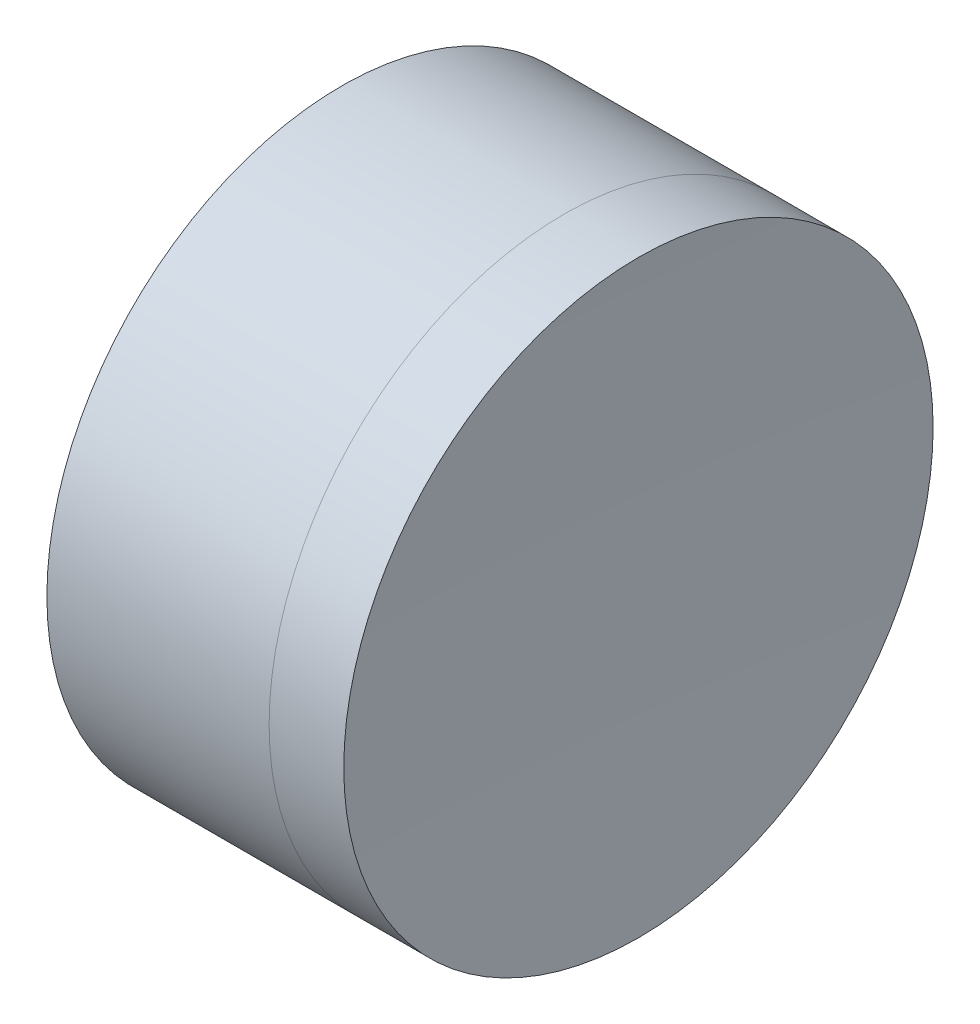
SolidWorks part; units mm, degrees
ref_plane "前视基准面" through (0, 0, 0) normal (0, 0, 1) x (1, 0, 0)
ref_plane "上视基准面" through (0, 0, 0) normal (0, 1, 0) x (1, 0, 0)
ref_plane "右视基准面" through (0, 0, 0) normal (1, 0, 0) x (0, 0, -1)
sketch "草图1" plane through (0, 0, 0) normal (0, 1, 0) x (1, 0, 0)
  line L0 (-185.2745, 0) -> (485.4408, 0) construction
  line L1 (160.6173, 6.35) -> (165.4061, 6.35)
  line L4 (160.6173, -6.35) -> (165.4061, -6.35)
  arc A0 (160.6173, -6.35) -> (160.6173, 6.35) centre (150.0832, 0) ccw
  arc A1 (165.4061, 6.35) -> (165.4061, -6.35) centre (177.8832, 0) ccw
  point P6 (162.3832, 0)
  point P8 (163.8832, 0)
  dimension "D3" = 6.35
  dimension "D4" = 1.5
  dimension "D1" = 12.3
  dimension "D5" = 14
  dimension "D2" = 6.35
revolve "旋转1" add sketch "草图1" angle 360 about L0
sketch "草图2" plane through (0, 0, 0) normal (0, 1, 0) x (1, 0, 0)
  line L2 (160.6173, 0) -> (272.9951, 0) construction
  line L3 (160.6173, -6.35) -> (160.6173, 6.35) construction
  line L6 (165.4061, 6.35) -> (167.0152, 6.35)
  line L7 (165.4061, -6.35) -> (167.0152, -6.35)
  arc A2 (165.4061, 6.35) -> (165.4061, -6.35) centre (177.8832, 0) ccw construction
  arc A3 (165.4061, 6.35) -> (165.4061, -6.35) centre (177.8832, 0) ccw
  arc A4 (167.0152, 6.35) -> (167.0152, -6.35) centre (319.6832, 0) ccw
  point P8 (163.8832, 0)
  point P9 (166.8832, 0)
  dimension "D1" = 3
  dimension "D2" = 152.8
revolve "旋转3" add sketch "草图2" angle 360 about L2
